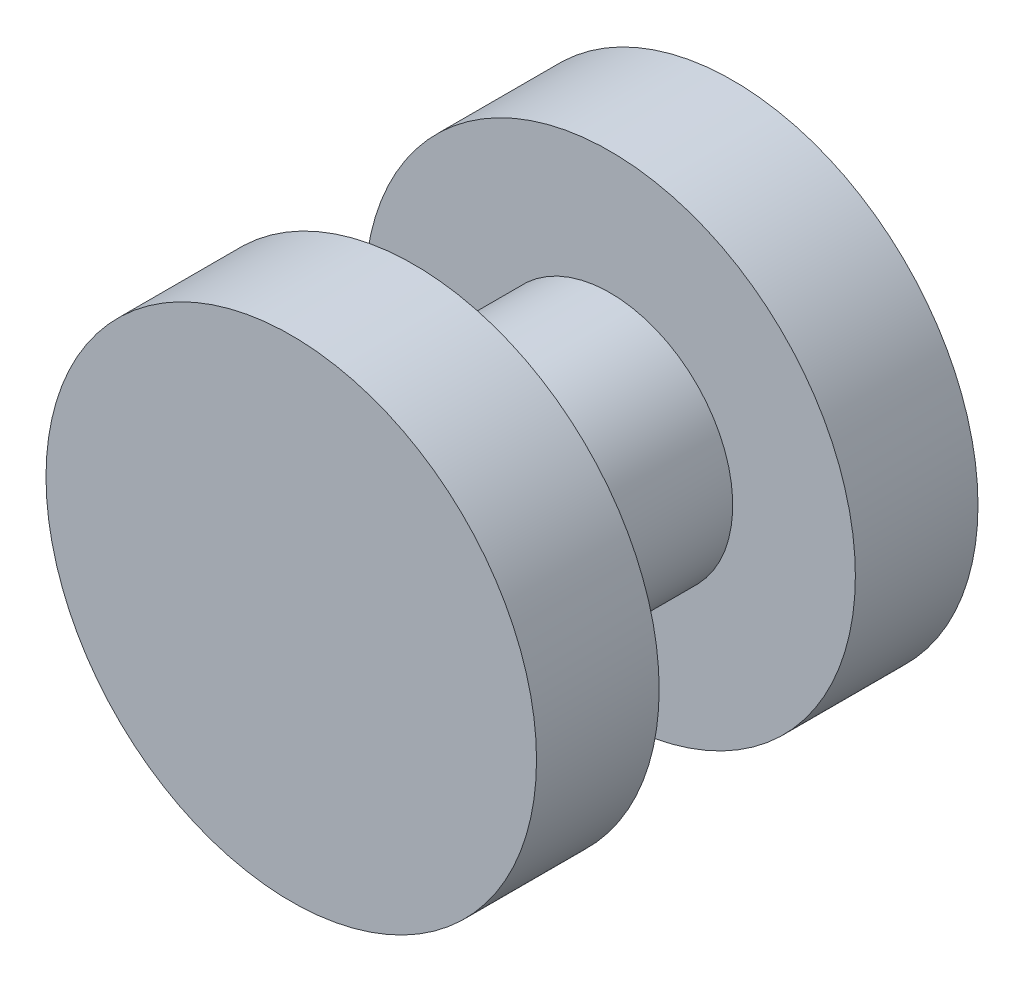
SolidWorks part; units mm, degrees
ref_plane "Front Plane" through (0, 0, 0) normal (0, 0, 1) x (1, 0, 0)
ref_plane "Top Plane" through (0, 0, 0) normal (0, 1, 0) x (1, 0, 0)
ref_plane "Right Plane" through (0, 0, 0) normal (1, 0, 0) x (0, 0, -1)
sketch "Sketch1" plane through (0, 0, 0) normal (0, 0, 1) x (1, 0, 0)
  circle A0 centre (0, 0) radius 3.175
  dimension "D1" = 6.35
extrude "Boss-Extrude1" add sketch "Sketch1" along normal blind 5.08
sketch "Sketch2" plane through (0, 0, 0) normal (0, 0, -1) x (-1, 0, 0)
  circle A0 centre (0, 0) radius 6.35
  dimension "D1" = 12.7
extrude "Boss-Extrude2" add sketch "Sketch2" along normal blind 3.175
sketch "Sketch3" plane through (0, 0, 5.08) normal (0, 0, 1) x (1, 0, 0)
  circle A0 centre (0, 0) radius 6.35
  dimension "D1" = 12.7
extrude "Boss-Extrude3" add sketch "Sketch3" along normal blind 3.175
